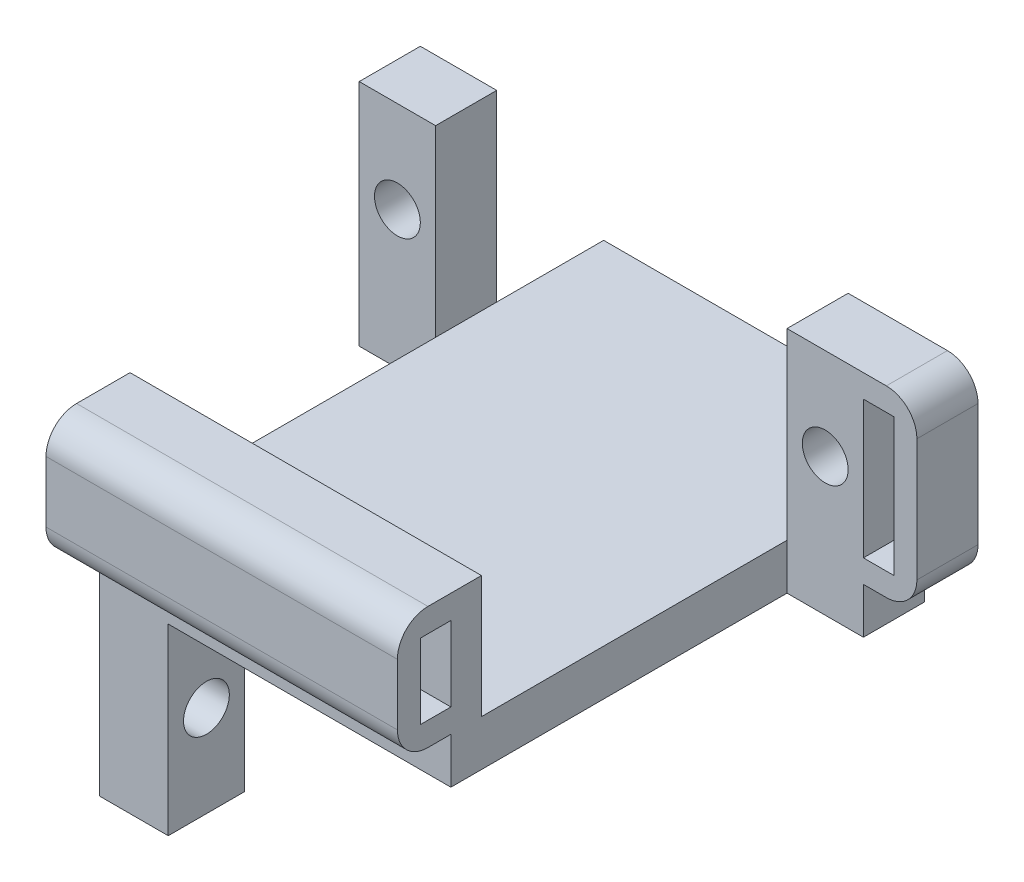
SolidWorks part; units mm, degrees
ref_plane "Front Plane" through (0, 0, 0) normal (0, 0, 1) x (1, 0, 0)
ref_plane "Top Plane" through (0, 0, 0) normal (0, 1, 0) x (1, 0, 0)
ref_plane "Right Plane" through (0, 0, 0) normal (1, 0, 0) x (0, 0, -1)
sketch "Sketch2" plane through (0, 0, 0) normal (0, 1, 0) x (1, 0, 0)
  line L0 (-11.5, 5.5) -> (-11.5, -16.5)
  line L1 (-11.5, -16.5) -> (11.5, -16.5)
  line L2 (11.5, 5.5) -> (11.5, -16.5)
  line L3 (11.5, 9.5) -> (16.5, 9.5)
  line L4 (11.5, 5.5) -> (16.5, 5.5)
  line L5 (16.5, 9.5) -> (16.5, 5.5)
  line L6 (-11.5, 9.5) -> (-16.5, 9.5)
  line L7 (-11.5, 5.5) -> (-16.5, 5.5)
  line L8 (-16.5, 9.5) -> (-16.5, 5.5)
  line L9 (-11.5, 9.5) -> (-11.5, 16.5)
  line L10 (-11.5, 16.5) -> (11.5, 16.5)
  line L11 (11.5, 9.5) -> (11.5, 16.5)
  dimension "D1" = 23
  dimension "D2" = 5
  dimension "D3" = 4
  dimension "D4" = 5
  dimension "D5" = 4
  dimension "D6" = 33
  dimension "D7" = 11
extrude "Boss-Extrude1" add sketch "Sketch2" along normal blind 3
sketch "Sketch3" plane through (0, 0, 0) normal (0, -1, 0) x (1, 0, 0)
  line L0 (11.5, -16.5) -> (-11.5, -16.5) construction
  line L1 (-11.5, 16.5) -> (-7, 16.5)
  line L2 (-11.5, 16.5) -> (-11.5, 11.5)
  line L3 (-11.5, 11.5) -> (-7, 11.5)
  line L4 (-7, 16.5) -> (-7, 11.5)
  line L5 (-11.5, -16.5) -> (-7, -16.5)
  line L6 (-11.5, -16.5) -> (-11.5, -11.5)
  line L7 (-11.5, -11.5) -> (-7, -11.5)
  line L8 (-7, -16.5) -> (-7, -11.5)
  dimension "D1" = 5
  dimension "D2" = 4.5
  dimension "D3" = 5
  dimension "D4" = 4.5
extrude "Boss-Extrude2" add sketch "Sketch3" along normal blind 12
sketch "Sketch4" plane through (0, 3, 0) normal (0, 1, 0) x (1, 0, 0)
  line L1 (-16.5, 9.5) -> (-11.5, 9.5)
  line L2 (-16.5, 9.5) -> (-16.5, 5.5)
  line L3 (-16.5, 5.5) -> (-11.5, 5.5)
  line L4 (-11.5, 9.5) -> (-11.5, 5.5)
  line L5 (16.5, 9.5) -> (11.5, 9.5)
  line L6 (16.5, 9.5) -> (16.5, 5.5)
  line L7 (16.5, 5.5) -> (11.5, 5.5)
  line L8 (11.5, 9.5) -> (11.5, 5.5)
extrude "Boss-Extrude3" add sketch "Sketch4" along normal blind 12
sketch "Sketch5" plane through (0, 0, -5.5) normal (0, 0, 1) x (1, 0, 0)
  line L0 (-11.5, 3) -> (-16.5, 15) construction
  line L1 (11.5, 3) -> (16.5, 15) construction
  circle A0 centre (14, 9) radius 1.5
  circle A1 centre (-14, 9) radius 1.5
  dimension "D1" = 3
  dimension "D2" = 3
extrude "Cut-Extrude1" cut sketch "Sketch5" against normal blind 12
sketch "Sketch6" plane through (-7, 0, 0) normal (1, 0, 0) x (0, 0, -1)
  line L0 (-16.5, -12) -> (-11.5, 0) construction
  line L1 (11.5, 0) -> (16.5, -12) construction
  circle A0 centre (-14, -6) radius 1.5
  circle A1 centre (14, -6) radius 1.5
  dimension "D1" = 3
  dimension "D2" = 3
extrude "Cut-Extrude2" cut sketch "Sketch6" against normal blind 12
sketch "Sketch7" plane through (0, 3, 0) normal (0, 1, 0) x (1, 0, 0)
  line L0 (-11.5, -16.5) -> (-11.5, -14.5) construction
  line L2 (-11.5, -14.5) -> (11.5, -14.5)
  line L3 (-11.5, -14.5) -> (-11.5, -20)
  line L4 (-11.5, -20) -> (11.5, -20)
  line L5 (11.5, -14.5) -> (11.5, -20)
  dimension "D1" = 2
  dimension "D2" = 23
  dimension "D3" = 5.5
extrude "Boss-Extrude5" add sketch "Sketch7" along normal blind 8
sketch "Sketch8" plane through (-11.5, 0, 0) normal (-1, 0, 0) x (0, 0, 1)
  line L0 (14.5, 11) -> (14.5, 3) construction
  line L1 (16.5, 9.45) -> (18.5, 9.45)
  line L2 (16.5, 9.45) -> (16.5, 4.55)
  line L3 (16.5, 4.55) -> (18.5, 4.55)
  line L4 (18.5, 9.45) -> (18.5, 4.55)
  line L5 (16.5, 3) -> (20, 3) construction
  line L6 (20, 11) -> (20, 3) construction
  line L7 (14.5, 11) -> (20, 11) construction
  dimension "D1" = 2
  dimension "D2" = 1.55
  dimension "D3" = 1.5
  dimension "D4" = 1.55
extrude "Cut-Extrude3" cut sketch "Sketch8" against normal blind 28
fillet "Fillet1" radius 2 2 edges at (0, 3, 20) (0, 11, 20)
sketch "Sketch11" plane through (16.5, 0, 0) normal (1, 0, 0) x (0, 0, -1)
  line L1 (5.5, 15) -> (9.5, 15)
  line L2 (5.5, 15) -> (5.5, 3)
  line L3 (5.5, 3) -> (9.5, 3)
  line L4 (9.5, 15) -> (9.5, 3)
extrude "Boss-Extrude6" add sketch "Sketch11" along normal blind 3.5
sketch "Sketch12" plane through (0, 0, -5.5) normal (0, 0, 1) x (1, 0, 0)
  line L0 (20, 15) -> (20, 3) construction
  line L1 (16.5, 13.5) -> (18.5, 13.5)
  line L2 (16.5, 13.5) -> (16.5, 4.5)
  line L3 (16.5, 4.5) -> (18.5, 4.5)
  line L4 (18.5, 13.5) -> (18.5, 4.5)
  line L5 (11.5, 15) -> (20, 15) construction
  line L6 (20, 3) -> (16.5, 3) construction
  dimension "D1" = 1.5
  dimension "D2" = 1.5
  dimension "D3" = 1.5
  dimension "D4" = 2
extrude "Cut-Extrude5" cut sketch "Sketch12" against normal blind 10
fillet "Fillet3" radius 2 2 edges at (20, 3, -7.5) (20, 15, -7.5)
